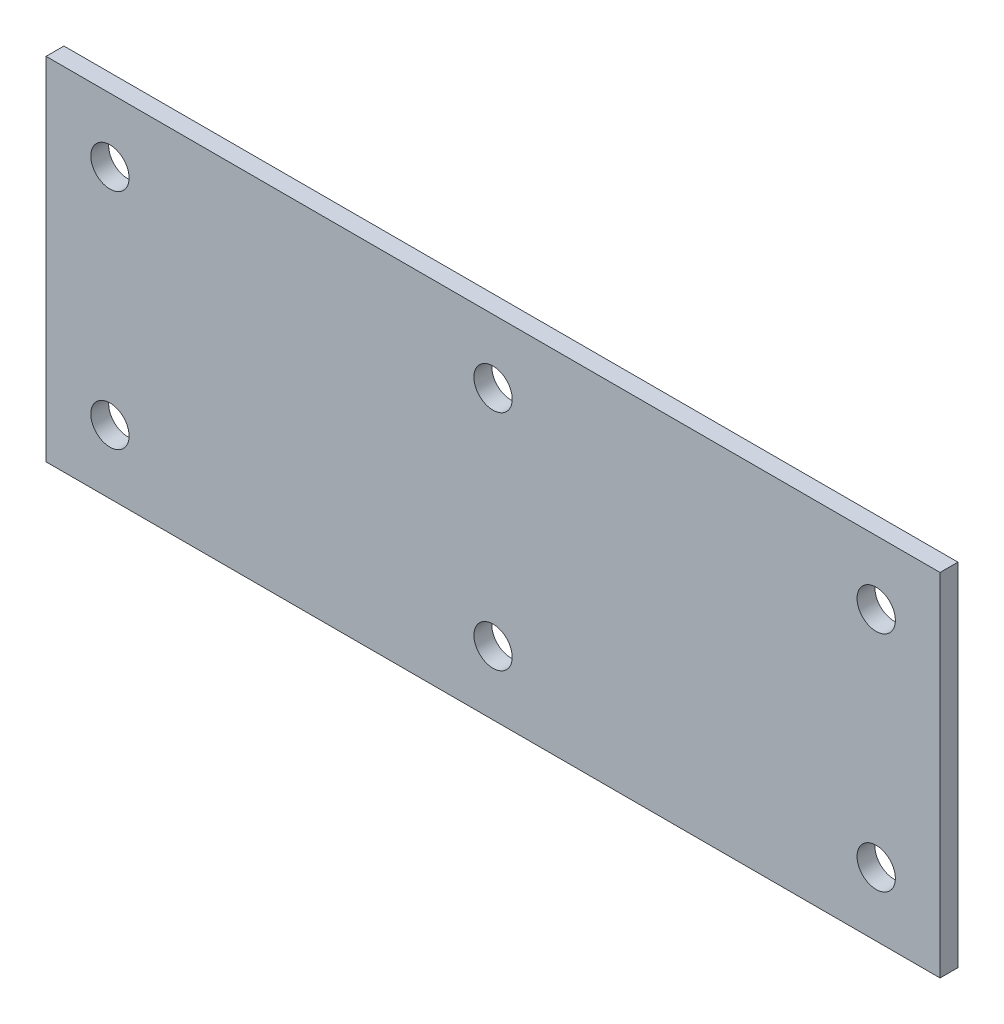
SolidWorks part; units mm, degrees
ref_plane "Front Plane" through (0, 0, 0) normal (0, 0, 1) x (1, 0, 0)
ref_plane "Top Plane" through (0, 0, 0) normal (0, 1, 0) x (1, 0, 0)
ref_plane "Right Plane" through (0, 0, 0) normal (1, 0, 0) x (0, 0, -1)
sketch "Sketch1" plane through (0, 0, 0) normal (0, 0, 1) x (1, 0, 0)
  line L1 (-44.45, 17.4625) -> (44.45, 17.4625)
  line L2 (-44.45, 17.4625) -> (-44.45, -17.4625)
  line L3 (-44.45, -17.4625) -> (44.45, -17.4625)
  line L4 (44.45, 17.4625) -> (44.45, -17.4625)
  line L5 (-44.45, 17.4625) -> (44.45, -17.4625) construction
  line L6 (-44.45, -17.4625) -> (44.45, 17.4625) construction
  point P0 (0, 0)
  dimension "D1" = 88.9
  dimension "D2" = 34.925
extrude "Boss-Extrude1" add sketch "Sketch1" along normal blind 1.778
sketch "Sketch2" plane through (0, 0, 1.778) normal (0, 0, 1) x (1, 0, 0)
  line L0 (0, -17.4625) -> (0, 17.4625) construction
  line L1 (-44.45, -17.4625) -> (44.45, -17.4625) construction
  line L2 (44.45, 17.4625) -> (-44.45, 17.4625) construction
  line L3 (-44.45, 0) -> (44.45, 0) construction
  line L4 (-44.45, 17.4625) -> (-44.45, -17.4625) construction
  line L5 (44.45, -17.4625) -> (44.45, 17.4625) construction
  circle A0 centre (0, 11.1125) radius 1.905
  circle A1 centre (-38.1, 11.1125) radius 1.905
  circle A2 centre (-38.1, -11.1125) radius 1.905
  circle A3 centre (0, -11.1125) radius 1.905
  circle A4 centre (38.1, -11.1125) radius 1.905
  circle A5 centre (38.1, 11.1125) radius 1.905
  point P17 (-38.1, 11.1125)
  dimension "D1" = 3.81
  dimension "D2" = 38.1
  dimension "D3" = 6.35
extrude "Cut-Extrude1" cut sketch "Sketch2" against normal through all
